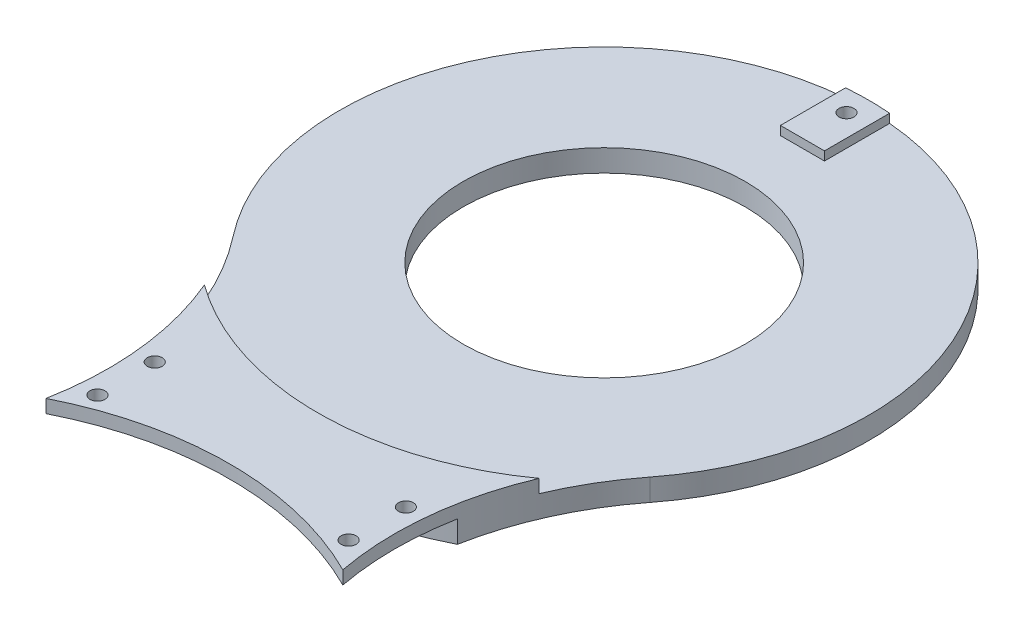
SolidWorks part; units mm, degrees
material "PLA"
ref_plane "Alzado" through (0, 0, 0) normal (0, 0, 1) x (1, 0, 0)
ref_plane "Planta" through (0, 0, 0) normal (0, 1, 0) x (1, 0, 0)
ref_plane "Vista lateral" through (0, 0, 0) normal (1, 0, 0) x (0, 0, -1)
sketch "Croquis1" plane through (0, 0, 0) normal (0, 1, 0) x (1, 0, 0)
  circle A0 centre (0, 0) radius 32
  arc A1 (-47.2936, 36.9231) -> (47.2936, 36.9231) centre (0, 0) ccw
  circle A2 centre (0, 160) radius 32
  arc A3 (47.2936, 123.0769) -> (-47.2936, 123.0769) centre (0, 160) ccw
  arc A4 (47.2936, 123.0769) -> (47.2936, 36.9231) centre (102.4695, 80) ccw
  arc A5 (-47.2936, 36.9231) -> (-47.2936, 123.0769) centre (-102.4695, 80) ccw
  dimension "D2" = 120
  dimension "D3" = 140
  dimension "D4" = 64
  dimension "D1" = 160
extrude "Saliente-Extruir1" add sketch "Croquis1" along normal blind 5
sketch "Croquis2" plane through (0, 5, 0) normal (0, 1, 0) x (1, 0, 0)
  line L1 (5, 205) -> (-5, 205)
  line L2 (5, 205) -> (5, 219.7913)
  line L4 (-5, 205) -> (-5, 219.7913)
  line L7 (-5, -45) -> (5, -45)
  line L8 (-5, -45) -> (-5, -59.7913)
  line L10 (5, -45) -> (5, -59.7913)
  circle A0 centre (0, 160) radius 32 construction
  arc A1 (-47.2936, 36.9231) -> (47.2936, 36.9231) centre (0, 0) ccw construction
  arc A2 (47.2936, 123.0769) -> (-47.2936, 123.0769) centre (0, 160) ccw construction
  arc A3 (-5, -59.7913) -> (5, -59.7913) centre (0, 0) ccw
  arc A4 (5, 219.7913) -> (-5, 219.7913) centre (0, 160) ccw
  point P0 (0, 205)
  point P6 (0, -45)
  dimension "D1" = 45
  dimension "D2" = 45
  dimension "D3" = 10
  dimension "D4" = 10
extrude "Saliente-Extruir2" add sketch "Croquis2" along normal blind 2
sketch "Croquis3" plane through (0, 7, 0) normal (0, 1, 0) x (1, 0, 0)
  circle A0 centre (0, 215) radius 1.7
  circle A1 centre (0, -55) radius 1.7
  circle A2 centre (0, 160) radius 32 construction
  dimension "D3" = 3.4
  dimension "D1" = 55
  dimension "D2" = 55
extrude "Cortar-Extruir1" cut sketch "Croquis3" against normal blind 19
sketch "Croquis4" plane through (0, 0, 0) normal (0, -1, 0) x (1, 0, 0)
  circle A0 centre (0, 55) radius 2.95
  circle A1 centre (0, -215) radius 2.95
  dimension "D1" = 5.9
extrude "Cortar-Extruir2" cut sketch "Croquis4" against normal blind 3
sketch "Croquis5" plane through (0, 0, 0) normal (0, -1, 0) x (1, 0, 0)
  line L0 (0, 0) -> (0, -160) construction
  line L1 (28.5, -86.5) -> (-28.5, -86.5) construction
  line L2 (28.5, -86.5) -> (28.5, -73.5) construction
  line L3 (28.5, -73.5) -> (-28.5, -73.5) construction
  line L4 (-28.5, -86.5) -> (-28.5, -73.5) construction
  line L5 (28.5, -86.5) -> (-28.5, -73.5) construction
  line L6 (28.5, -73.5) -> (-28.5, -86.5) construction
  circle A0 centre (-28.5, -73.5) radius 1.7
  circle A1 centre (-28.5, -86.5) radius 1.7
  circle A2 centre (28.5, -86.5) radius 1.7
  circle A3 centre (28.5, -73.5) radius 1.7
  point P0 (0, -80)
  point P10 (0, -80)
  dimension "D1" = 3.4
  dimension "D2" = 13
  dimension "D3" = 57
extrude "Cortar-Extruir3" cut sketch "Croquis5" against normal blind 5
sketch "Croquis6" plane through (0, 0, 0) normal (0, -1, 0) x (1, 0, 0)
  line L1 (65, 77.4166) -> (-65, 77.4166)
  line L2 (65, 77.4166) -> (65, -122.5834)
  line L4 (-65, 77.4166) -> (-65, -122.5834)
  line L5 (65, 77.4166) -> (-65, -122.5834) construction
  line L6 (65, -122.5834) -> (-65, 77.4166) construction
  arc A0 (65, -122.5834) -> (-65, -122.5834) centre (0, -160) ccw
  point P3 (0, 0)
  dimension "D1" = 75
  dimension "D2" = 200
  dimension "D3" = 130
extrude "Cortar-Extruir5" cut sketch "Croquis6" against normal blind 37
sketch "Croquis7" plane through (0, 5, 0) normal (0, 1, 0) x (1, 0, 0)
  arc A0 (47.2936, 123.0769) -> (33.6854, 92.9904) centre (102.4695, 80) ccw construction
  arc A1 (-33.6854, 92.9904) -> (-47.2936, 123.0769) centre (-102.4695, 80) ccw construction
  arc A2 (37.9965, 107.2623) -> (33.6854, 67.0096) centre (102.4695, 80) ccw
  arc A3 (-33.6854, 67.0096) -> (-37.9965, 107.2623) centre (-102.4695, 80) ccw
  arc A4 (-37.9965, 107.2623) -> (37.9965, 107.2623) centre (0, 160) ccw
  arc A5 (33.6854, 67.0096) -> (-33.6854, 67.0096) centre (0, 0) ccw
  circle A10 centre (-28.5, 86.5) radius 1.7 construction
  circle A19 centre (-28.5, 73.5) radius 1.7 construction
  circle A20 centre (28.5, 73.5) radius 1.7 construction
  circle A21 centre (28.5, 86.5) radius 1.7 construction
  circle A22 centre (-28.5, 86.5) radius 1.7
  circle A23 centre (-28.5, 73.5) radius 1.7
  circle A24 centre (28.5, 73.5) radius 1.7
  circle A25 centre (28.5, 86.5) radius 1.7
  dimension "D1" = 150
  dimension "D2" = 130
extrude "Saliente-Extruir3" add sketch "Croquis7" along normal blind 3
